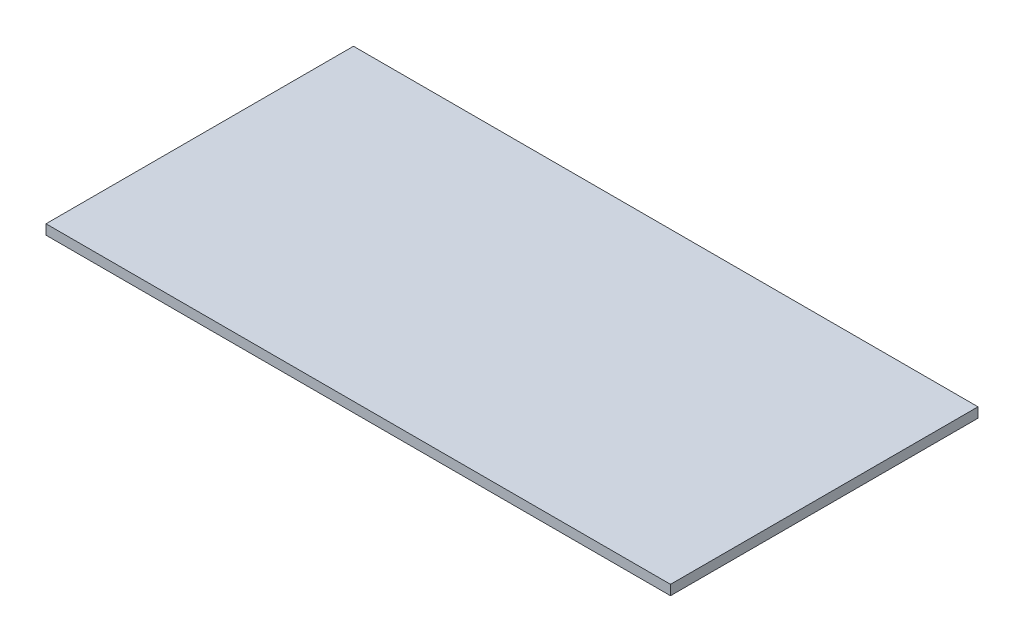
SolidWorks part; units mm, degrees
ref_plane "Front Plane" through (0, 0, 0) normal (0, 0, 1) x (1, 0, 0)
ref_plane "Top Plane" through (0, 0, 0) normal (0, 1, 0) x (1, 0, 0)
ref_plane "Right Plane" through (0, 0, 0) normal (1, 0, 0) x (0, 0, -1)
sketch "Sketch1" plane through (0, 0, 0) normal (0, 1, 0) x (1, 0, 0)
  line L1 (-63, -31.02) -> (63, -31.02)
  line L2 (-63, -31.02) -> (-63, 31.02)
  line L3 (-63, 31.02) -> (63, 31.02)
  line L4 (63, -31.02) -> (63, 31.02)
  line L5 (-63, -31.02) -> (63, 31.02) construction
  line L6 (-63, 31.02) -> (63, -31.02) construction
  point P0 (0, 0)
  dimension "D1" = 126
  dimension "D2" = 62.04
extrude "Boss-Extrude1" add sketch "Sketch1" along normal blind 2
